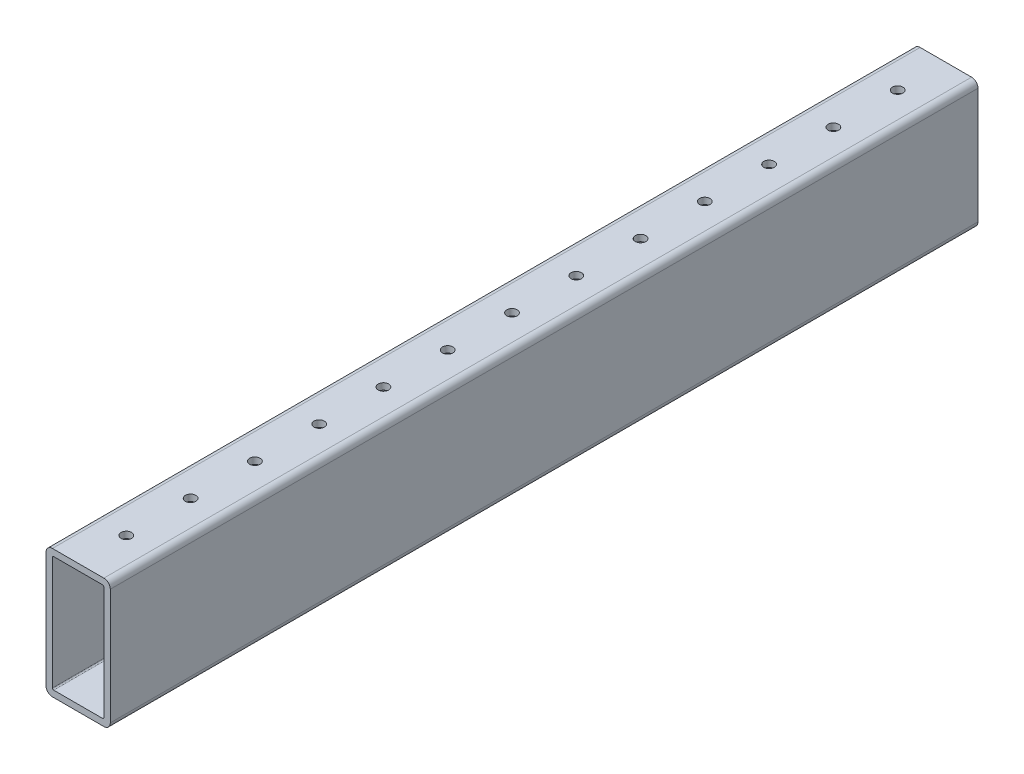
SolidWorks part; units mm, degrees
ref_plane "Front Plane" through (0, 0, 0) normal (0, 0, 1) x (1, 0, 0)
ref_plane "Top Plane" through (0, 0, 0) normal (0, 1, 0) x (1, 0, 0)
ref_plane "Right Plane" through (0, 0, 0) normal (1, 0, 0) x (0, 0, -1)
ref_plane "Plane1" through (12.7, 0, 0) normal (1, 0, 0) x (0, 0, -1)
sketch "Sketch1" plane through (12.7, 0, 0) normal (1, 0, 0) x (0, 0, -1)
  line L0 (171.45, -25.4) -> (171.45, 25.4)
  line L1 (171.45, 25.4) -> (-171.45, 25.4)
  line L2 (-171.45, 25.4) -> (-171.45, -25.4)
  line L3 (-171.45, -25.4) -> (171.45, -25.4)
  point P5 (0, 25.4)
  dimension "D1" = 50.8
  dimension "D2" = 25.4
  dimension "D3" = 342.9
extrude "Boss-Extrude1" add sketch "Sketch1" against normal blind 25.4
sketch "Sketch2" plane through (0, 0, -171.45) normal (0, 0, -1) x (-1, 0, 0)
  line L0 (10.16, -22.86) -> (10.16, 22.86)
  line L1 (10.16, 22.86) -> (-10.16, 22.86)
  line L2 (-10.16, 22.86) -> (-10.16, -22.86)
  line L3 (-10.16, -22.86) -> (10.16, -22.86)
extrude "Cut-Extrude1" cut sketch "Sketch2" against normal through all
hole_wizard "#6 Clearance Hole1" positions "Sketch4" profile "Sketch3" hole size "#6" standard "ANSI Inch"
sketch "Sketch4" plane through (0, -25.4, 0) normal (0, -1, 0) x (-1, 0, 0)
  point P0 (0, 711.2)
  point P1 (0, 736.6)
  point P2 (0, 685.8)
  point P3 (0, 660.4)
  point P4 (0, 635)
  point P5 (0, 609.6)
  point P6 (0, 584.2)
  point P7 (0, 558.8)
  point P8 (0, 533.4)
  point P9 (0, 508)
  point P10 (0, 482.6)
  point P11 (0, 457.2)
  point P12 (0, 431.8)
  point P13 (0, 406.4)
  point P14 (0, 381)
  point P15 (0, 355.6)
  point P16 (0, 330.2)
  point P17 (0, 304.8)
  point P18 (0, 279.4)
  point P19 (0, 254)
  point P20 (0, 228.6)
  point P21 (0, 203.2)
  point P22 (0, 177.8)
  point P23 (0, 152.4)
  point P24 (0, 127)
  point P25 (0, 101.6)
  point P26 (0, 76.2)
  point P27 (0, 50.8)
  point P28 (0, 25.4)
  point P29 (0, 0)
  point P30 (0, -25.4)
  point P31 (0, -50.8)
  point P32 (0, -76.2)
  point P33 (0, -101.6)
  point P34 (0, -127)
  point P35 (0, -152.4)
  point P36 (0, -177.8)
  point P37 (0, -203.2)
  point P38 (0, -228.6)
  point P39 (0, -254)
  point P40 (0, -279.4)
  point P41 (0, -304.8)
  point P42 (0, -330.2)
  point P43 (0, -355.6)
  point P44 (0, -381)
  point P45 (0, -406.4)
  point P46 (0, -431.8)
  point P47 (0, -457.2)
  point P48 (0, -482.6)
  point P49 (0, -508)
  point P50 (0, -533.4)
  point P51 (0, -558.8)
  point P52 (0, -584.2)
  point P53 (0, -609.6)
  point P54 (0, -635)
  point P55 (0, -660.4)
  point P56 (0, -685.8)
  point P57 (0, -711.2)
  point P58 (0, -736.6)
sketch "Sketch3" plane through (0, -25.4, -711.2) normal (1, 0, 0) x (0, 0, -1)
  line L0 (0, 0) -> (0, 50.8)
  line L1 (0, 50.8) -> (2.0701, 50.8)
  line L2 (2.0701, 50.8) -> (2.0701, 0)
  line L5 (2.0701, 0) -> (0, 0)
  line L11 (0, -6.35) -> (0, 107.95) construction
  dimension "Thru Hole Dia." = 4.1402
  dimension "Thru Hole Depth" = 50.8
hole_wizard "#6 Clearance Hole2" positions "Sketch6" profile "Sketch5" hole size "#6" standard "ANSI Inch"
sketch "Sketch6" plane through (0, 25.4, 0) normal (0, 1, 0) x (1, 0, 0)
  point P0 (0, 711.2)
  point P1 (0, 736.6)
  point P2 (0, 685.8)
  point P3 (0, 660.4)
  point P4 (0, 635)
  point P5 (0, 609.6)
  point P6 (0, 584.2)
  point P7 (0, 558.8)
  point P8 (0, 533.4)
  point P9 (0, 508)
  point P10 (0, 482.6)
  point P11 (0, 457.2)
  point P12 (0, 431.8)
  point P13 (0, 406.4)
  point P14 (0, 381)
  point P15 (0, 355.6)
  point P16 (0, 330.2)
  point P17 (0, 304.8)
  point P18 (0, 279.4)
  point P19 (0, 254)
  point P20 (0, 228.6)
  point P21 (0, 203.2)
  point P22 (0, 177.8)
  point P23 (0, 152.4)
  point P24 (0, 127)
  point P25 (0, 101.6)
  point P26 (0, 76.2)
  point P27 (0, 50.8)
  point P28 (0, 25.4)
  point P29 (0, 0)
  point P30 (0, -25.4)
  point P31 (0, -50.8)
  point P32 (0, -76.2)
  point P33 (0, -101.6)
  point P34 (0, -127)
  point P35 (0, -152.4)
  point P36 (0, -177.8)
  point P37 (0, -203.2)
  point P38 (0, -228.6)
  point P39 (0, -254)
  point P40 (0, -279.4)
  point P41 (0, -304.8)
  point P42 (0, -330.2)
  point P43 (0, -355.6)
  point P44 (0, -381)
  point P45 (0, -406.4)
  point P46 (0, -431.8)
  point P47 (0, -457.2)
  point P48 (0, -482.6)
  point P49 (0, -508)
  point P50 (0, -533.4)
  point P51 (0, -558.8)
  point P52 (0, -584.2)
  point P53 (0, -609.6)
  point P54 (0, -635)
  point P55 (0, -660.4)
  point P56 (0, -685.8)
  point P57 (0, -711.2)
  point P58 (0, -736.6)
sketch "Sketch5" plane through (0, 25.4, -711.2) normal (1, 0, 0) x (0, 0, 1)
  line L0 (0, 0) -> (0, 50.8)
  line L1 (0, 50.8) -> (2.0701, 50.8)
  line L2 (2.0701, 50.8) -> (2.0701, 0)
  line L5 (2.0701, 0) -> (0, 0)
  line L11 (0, -6.35) -> (0, 107.95) construction
  dimension "Thru Hole Dia." = 4.1402
  dimension "Thru Hole Depth" = 50.8
fillet "Fillet1" radius 0.5 4 edges at (10.16, 22.86, 0) (-10.16, -22.86, 0) (-10.16, 22.86, 0) (10.16, -22.86, 0)
fillet "Fillet2" radius 2.54 4 edges at (12.7, 25.4, 0) (-12.7, -25.4, 0) (12.7, -25.4, 0) (-12.7, 25.4, 0)
